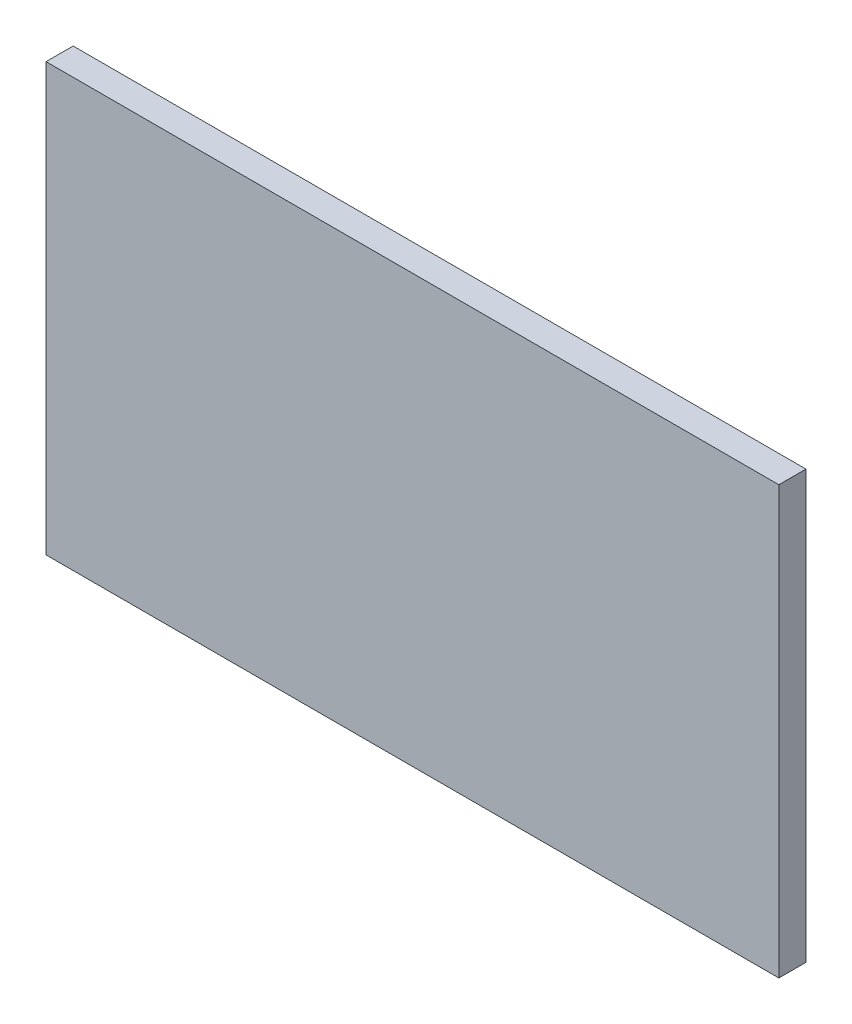
SolidWorks part; units mm, degrees
ref_plane "Plan de face" through (0, 0, 0) normal (0, 0, 1) x (1, 0, 0)
ref_plane "Plan de dessus" through (0, 0, 0) normal (0, 1, 0) x (1, 0, 0)
ref_plane "Plan de droite" through (0, 0, 0) normal (1, 0, 0) x (0, 0, -1)
sketch "Esquisse1" plane through (0, 0, 0) normal (0, 0, 1) x (1, 0, 0)
  line L1 (0, 0) -> (81.079, 0)
  line L2 (0, 0) -> (0, -47.2659)
  line L3 (0, -47.2659) -> (81.079, -47.2659)
  line L4 (81.079, 0) -> (81.079, -47.2659)
  dimension "D1" = 81.079
  dimension "D2" = 47.2659
extrude "Boss.-Extru.1" add sketch "Esquisse1" along normal blind 3
